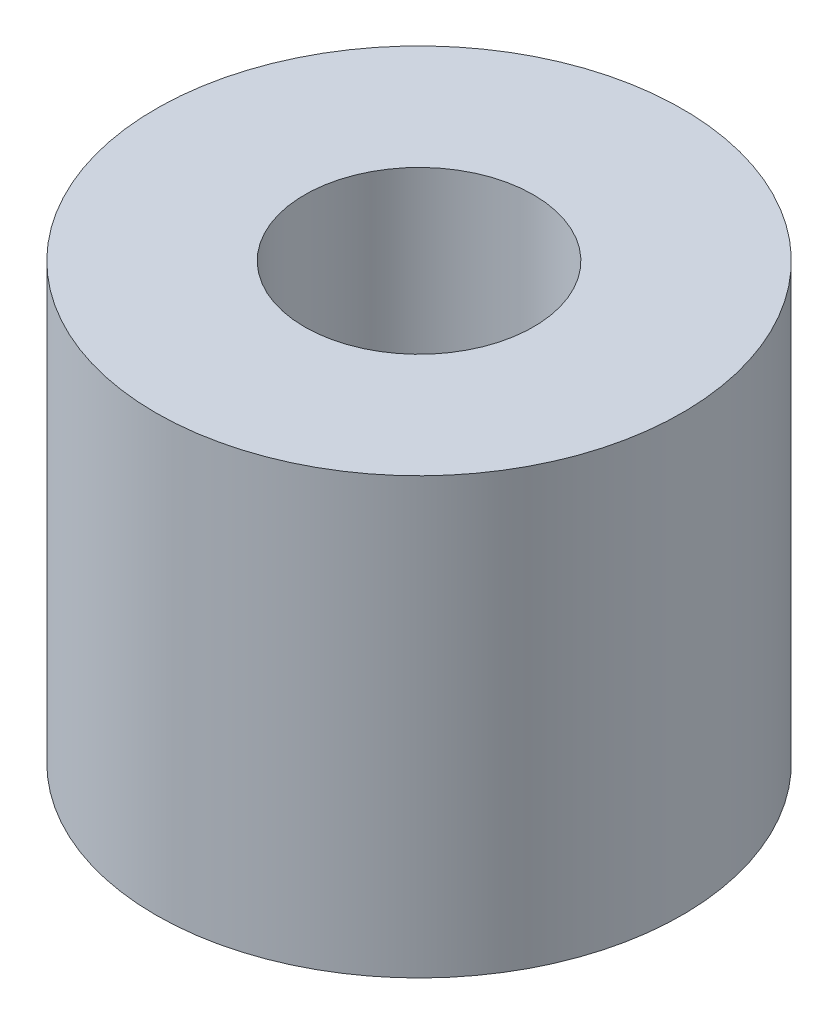
SolidWorks part; units mm, degrees
ref_plane "Front" through (0, 0, 0) normal (0, 0, 1) x (1, 0, 0)
ref_plane "Top" through (0, 0, 0) normal (0, 1, 0) x (1, 0, 0)
ref_plane "Right" through (0, 0, 0) normal (1, 0, 0) x (0, 0, -1)
sketch "Sketch1" plane through (0, 0, 0) normal (0, 1, 0) x (1, 0, 0)
  circle A0 centre (0, 0) radius 11.5
  dimension "D1" = 23
extrude "Boss-Extrude1" add sketch "Sketch1" along normal blind 19
sketch "Sketch2" plane through (0, 19, 0) normal (0, 1, 0) x (1, 0, 0)
  circle A0 centre (0, 0) radius 5
  dimension "D1" = 10
extrude "Cut-Extrude1" cut sketch "Sketch2" against normal through all
